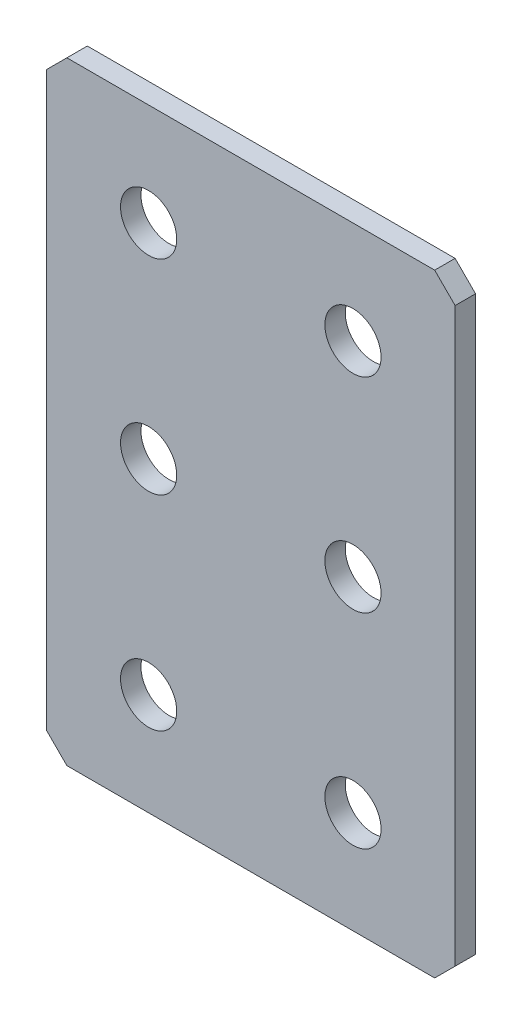
SolidWorks part; units mm, degrees
material "Простая углеродистая сталь"
ref_plane "Спереди(Плоскость XY)" through (0, 0, 0) normal (0, 0, 1) x (1, 0, 0)
ref_plane "Сверху(Плоскость XZ)" through (0, 0, 0) normal (0, 1, 0) x (1, 0, 0)
ref_plane "Справа(Плоскость ZY)" through (0, 0, 0) normal (1, 0, 0) x (0, 0, -1)
sketch "Эскиз1" plane through (0, 0, 0) normal (0, 0, 1) x (1, 0, 0)
  line L1 (-20, -30) -> (20, -30)
  line L2 (-20, -30) -> (-20, 30)
  line L3 (-20, 30) -> (20, 30)
  line L4 (20, -30) -> (20, 30)
  line L5 (-20, -30) -> (20, 30) construction
  line L6 (-20, 30) -> (20, -30) construction
  point P0 (0, 0)
  dimension "D1" = 40
  dimension "D2" = 60
extrude "Бобышка-Вытянуть1" add sketch "Эскиз1" along normal blind 2
chamfer "Фаска1" distance 2 angle 45 4 edges at (-20, -30, 1) (20, -30, 1) (-20, 30, 1) (20, 30, 1)
hole_wizard "Отверстие с зазором M51" positions "Эскиз2" profile "Эскиз3" hole size "M5" standard "DIN" end condition through all
sketch "Эскиз2" plane through (0, 0, 2) normal (0, 0, 1) x (1, 0, 0)
  line L0 (10, 0) -> (-10, 0) construction
  point P0 (-10, 20)
  point P2 (10, 20)
  point P4 (10, 0)
  point P6 (-10, 0)
  point P8 (-10, -20)
  point P10 (10, -20)
  dimension "D1" = 20
  dimension "D2" = 20
  dimension "D3" = 20
sketch "Эскиз3" plane through (-10, 20, 2) normal (1, 0, 0) x (0, -1, 0)
  line L0 (0, 0) -> (0, 2)
  line L1 (0, 2) -> (2.75, 2)
  line L2 (2.75, 2) -> (2.75, 0)
  line L5 (2.75, 0) -> (0, 0)
  line L11 (0, -6.35) -> (0, 107.95) construction
  dimension "Диаметр сквозного отверстия" = 5.5
  dimension "Глубина сквозного отверстия" = 2
